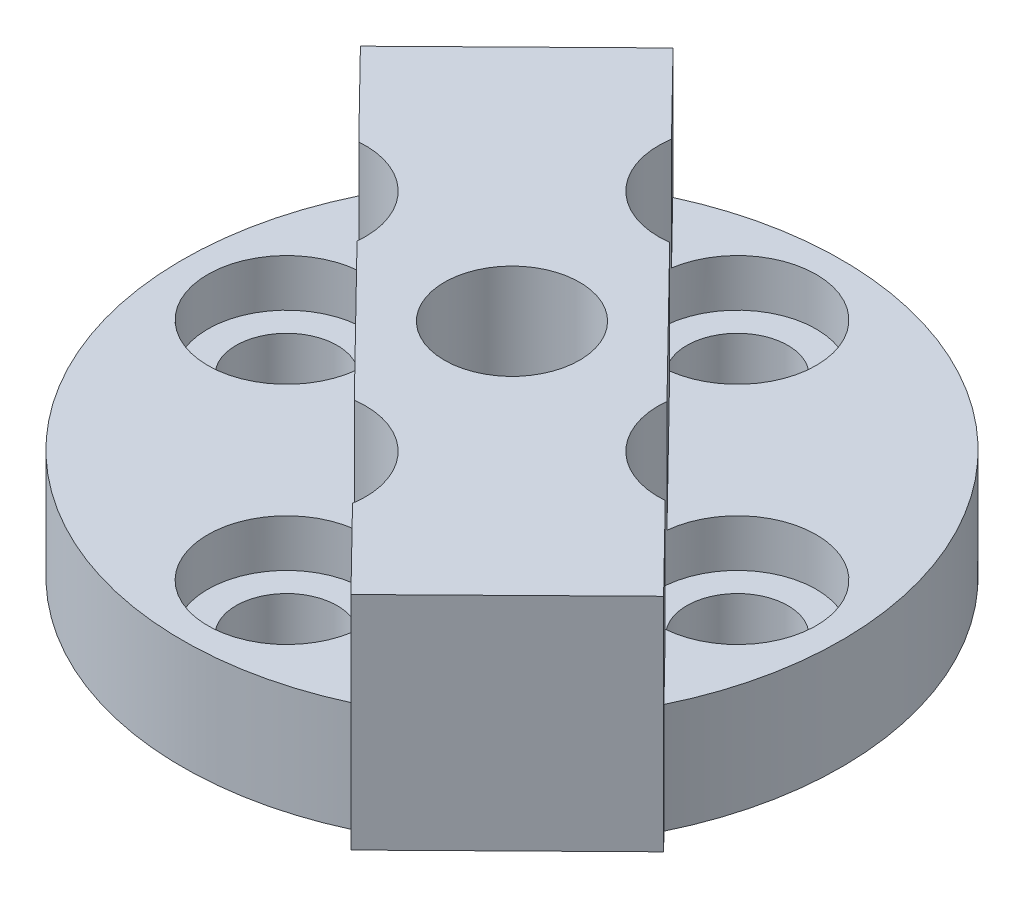
SolidWorks part; units mm, degrees
ref_plane "Front Plane" through (0, 0, 0) normal (0, 0, 1) x (1, 0, 0)
ref_plane "Top Plane" through (0, 0, 0) normal (0, 1, 0) x (1, 0, 0)
ref_plane "Right Plane" through (0, 0, 0) normal (1, 0, 0) x (0, 0, -1)
sketch "Sketch1" plane through (0, 0, 0) normal (0, 1, 0) x (1, 0, 0)
  circle A0 centre (0, 0) radius 18.5738
  circle A1 centre (0, 0) radius 12.7 construction
  circle A2 centre (0, 12.7) radius 2.8511
  circle A3 centre (-12.7, 0) radius 2.8511
  circle A4 centre (0, -12.7) radius 2.8511
  circle A5 centre (12.7, 0) radius 2.8511
  dimension "D1" = 37.1475
  dimension "D2" = 25.4
  dimension "D3" = 5.7023
extrude "Boss-Extrude1" add sketch "Sketch1" along normal blind 6.1849
sketch "Sketch2" plane through (0, 0, 0) normal (0, 1, 0) x (1, 0, 0)
  line L0 (-8.7979, 17.874) -> (-4.3927, 13.38)
  line L1 (-8.7979, 17.874) -> (-17.695, 9.1527)
  line L2 (17.695, -9.1527) -> (8.7979, -17.874)
  line L3 (-17.695, 9.1527) -> (-13.0655, 4.4299)
  line L4 (13.002, -13.264) -> (-13.002, 13.264) construction
  line L5 (-13.264, -13.002) -> (13.264, 13.002) construction
  line L6 (-8.2782, -0.4538) -> (-0.5923, -8.2946)
  line L7 (4.3927, -13.38) -> (8.7979, -17.874)
  line L8 (13.0655, -4.4299) -> (17.695, -9.1527)
  line L9 (0.5923, 8.2946) -> (8.2782, 0.4538)
  circle A0 centre (0, -12.7) radius 2.8492 construction
  circle A1 centre (12.7, 0) radius 2.8511 construction
  circle A3 centre (12.7, 0) radius 2.8511 construction
  circle A4 centre (0, 12.7) radius 2.8512 construction
  circle A5 centre (0, 12.7) radius 2.8512 construction
  arc A9 (-4.3927, 13.38) -> (0.5923, 8.2946) centre (0, 12.7) ccw
  arc A10 (8.2782, 0.4538) -> (13.0655, -4.4299) centre (12.7, 0) ccw
  arc A11 (4.3927, -13.38) -> (-0.5923, -8.2946) centre (0, -12.7) ccw
  arc A12 (-8.2782, -0.4538) -> (-13.0655, 4.4299) centre (-12.7, 0) ccw
  circle A13 centre (0, 0) radius 18.5738 construction
  point P30 (0, 0)
  point P38 (0, 0)
  dimension "D2" = 8.89
  dimension "D5" = 5.6985
  dimension "D1" = 12.4587
  dimension "D3" = 37.846
  dimension "D4" = 6.6134
extrude "Boss-Extrude2" add sketch "Sketch2" along normal blind 12.4714
sketch "Sketch3" plane through (0, 6.1849, 0) normal (0, 1, 0) x (1, 0, 0)
  circle A0 centre (0, -12.7) radius 4.445
  dimension "D1" = 8.89
extrude "Cut-Extrude1" cut sketch "Sketch3" against normal blind 2.667
pattern_circular "CirPattern1" count 4 over 360 about axis through (0, 6.1849, 0) along (0, -1, 0) of "Cut-Extrude1"
sketch "Sketch4" plane through (0, 12.4714, 0) normal (0, 1, 0) x (1, 0, 0)
  circle A0 centre (0, 0) radius 3.81
  dimension "D1" = 7.62
extrude "Cut-Extrude2" cut sketch "Sketch4" against normal blind 5.715
sketch "Sketch5" plane through (0, 6.7564, 0) normal (0, 1, 0) x (1, 0, 0)
  circle A0 centre (0, 0) radius 3.175
  dimension "D1" = 6.35
extrude "Cut-Extrude3" cut sketch "Sketch5" against normal through all
